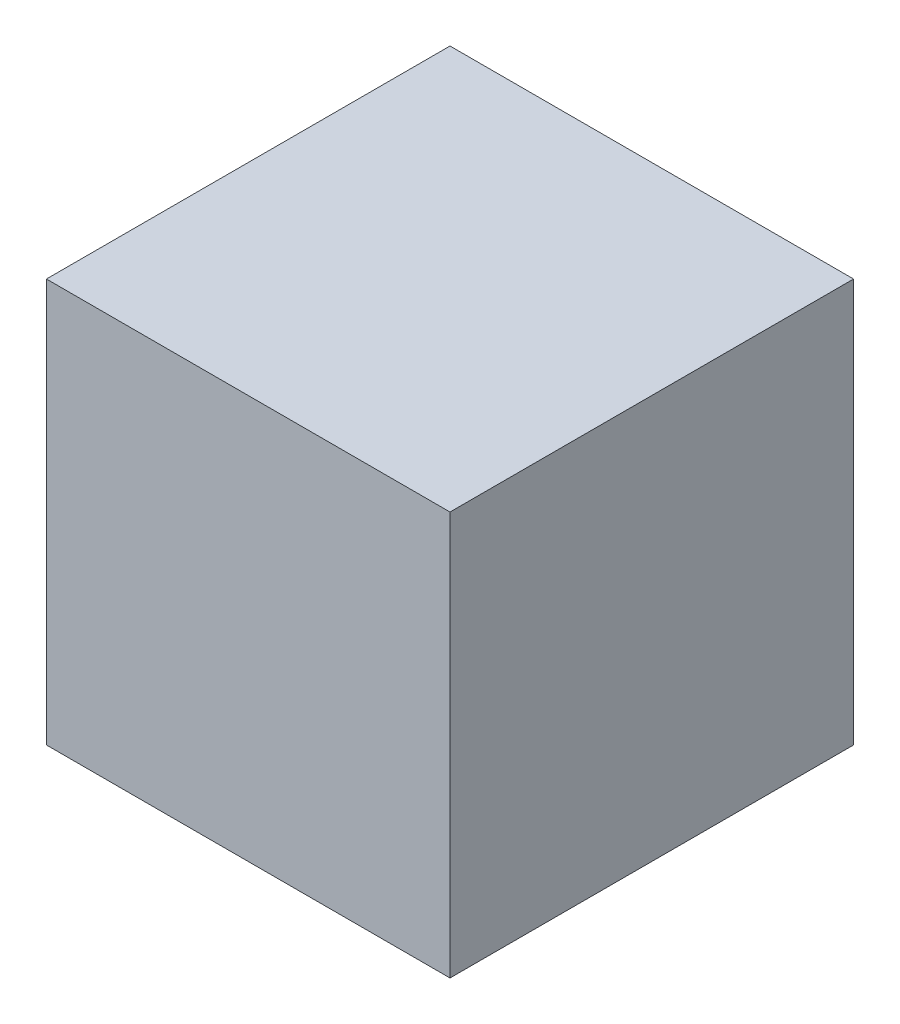
SolidWorks part; units mm, degrees
ref_plane "前视基准面" through (0, 0, 0) normal (0, 0, 1) x (1, 0, 0)
ref_plane "上视基准面" through (0, 0, 0) normal (0, 1, 0) x (1, 0, 0)
ref_plane "右视基准面" through (0, 0, 0) normal (1, 0, 0) x (0, 0, -1)
sketch "草图1" plane through (0, 0, 0) normal (0, 1, 0) x (1, 0, 0)
  line L1 (0, 0) -> (70, 0)
  line L2 (0, 0) -> (0, 70)
  line L3 (0, 70) -> (70, 70)
  line L4 (70, 0) -> (70, 70)
  line L5 (0, 0) -> (70, 70) construction
  line L6 (0, 70) -> (70, 0) construction
  point P4 (35, 35)
extrude "凸台-拉伸1" add sketch "草图1" along normal blind 70
